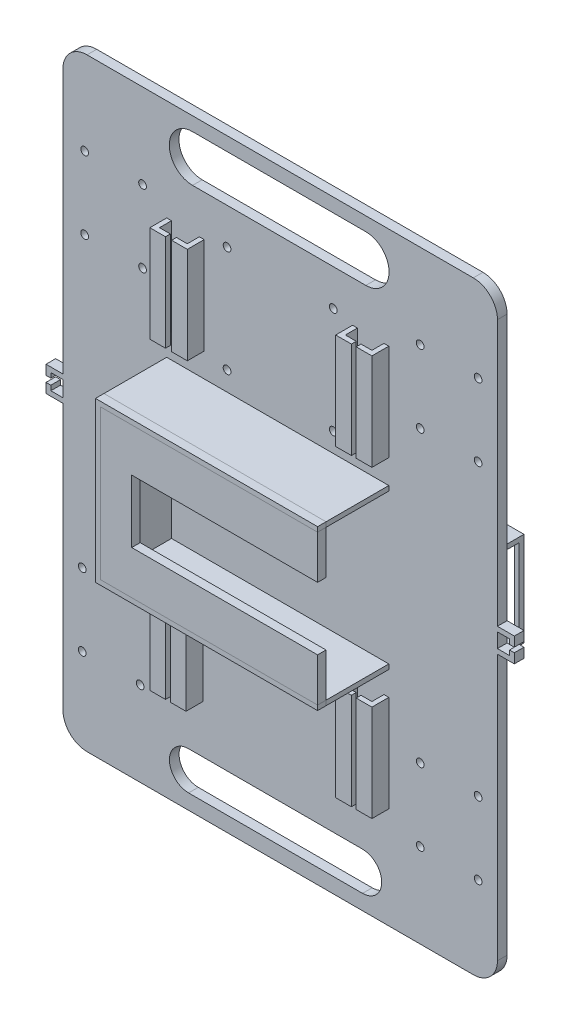
SolidWorks part; units mm, degrees
ref_plane "前视基准面" through (0, 0, 0) normal (0, 0, 1) x (1, 0, 0)
ref_plane "上视基准面" through (0, 0, 0) normal (0, 1, 0) x (1, 0, 0)
ref_plane "右视基准面" through (0, 0, 0) normal (1, 0, 0) x (0, 0, -1)
sketch "草图2" plane through (0, 0, 0) normal (0, 0, 1) x (1, 0, 0)
  line L0 (-107.1807, -135.5134) -> (-66.1807, -135.5134) construction
  line L1 (-97.1807, 63.077) -> (62.8193, 63.077)
  line L2 (-107.1807, 53.077) -> (-107.1807, -176.923)
  line L3 (-97.1807, -186.923) -> (62.8193, -186.923)
  line L4 (72.8193, 53.077) -> (72.8193, -176.923)
  line L5 (-92.3948, -186.923) -> (-92.3948, -116.923) construction
  line L6 (-85.9477, -186.923) -> (-85.9477, -156.923) construction
  line L7 (-107.1807, -156.923) -> (-66.1807, -156.923) construction
  line L8 (-107.1807, -116.923) -> (-66.1807, -116.923) construction
  line L9 (-66.1807, -116.923) -> (-66.1807, -156.923) construction
  line L10 (-66.1807, -156.923) -> (-107.1807, -156.923) construction
  line L11 (-107.1807, -156.923) -> (-107.1807, -116.923) construction
  line L12 (-107.1807, -156.923) -> (-107.1807, -158.923) construction
  line L13 (-107.1807, -152.2152) -> (-99.1807, -152.2152) construction
  line L14 (-99.1807, -156.923) -> (-99.1807, -151.923) construction
  line L15 (-99.1807, -151.923) -> (-99.1807, -121.923) construction
  line L16 (-99.1807, -121.923) -> (-75.1807, -121.923) construction
  line L17 (-75.1807, -121.923) -> (-75.1807, -151.923) construction
  line L18 (-66.1807, -156.923) -> (72.8193, -156.923) construction
  line L19 (-99.1807, -151.923) -> (72.8193, -151.923) construction
  line L20 (-99.1807, -121.923) -> (72.8193, -121.923) construction
  line L21 (72.8193, -151.923) -> (64.8193, -151.923) construction
  line L22 (64.8193, -151.923) -> (40.8193, -151.923) construction
  line L23 (40.8193, -151.923) -> (40.8193, -121.923) construction
  line L24 (40.8193, -121.923) -> (64.8193, -121.923) construction
  line L25 (64.8193, -121.923) -> (64.8193, -151.923) construction
  line L26 (-97.1807, 63.077) -> (-97.1807, 33.077) construction
  line L27 (-97.1807, 33.077) -> (-97.1807, -6.923) construction
  line L28 (-107.1807, 33.077) -> (-98.1807, 33.077) construction
  line L29 (-98.1807, 33.077) -> (-98.1807, 28.077) construction
  line L30 (-98.1807, 28.077) -> (-98.1807, -1.923) construction
  line L31 (-98.1807, 28.077) -> (-74.1807, 28.077) construction
  line L32 (-74.1807, 28.077) -> (-74.1807, -1.923) construction
  line L33 (-98.1807, -1.923) -> (-74.1807, -1.923) construction
  line L34 (-74.1807, 28.077) -> (72.8193, 28.077) construction
  line L35 (-74.1807, -1.923) -> (72.8193, -1.923) construction
  line L36 (40.8193, -121.923) -> (40.8193, 28.077) construction
  line L37 (64.8193, -121.923) -> (64.8193, 28.077) construction
  arc A0 (-97.1807, 63.077) -> (-107.1807, 53.077) centre (-97.1807, 53.077) ccw
  arc A1 (62.8193, 63.077) -> (72.8193, 53.077) centre (62.8193, 53.077) cw
  arc A2 (-107.1807, -176.923) -> (-97.1807, -186.923) centre (-97.1807, -176.923) ccw
  arc A3 (62.8193, -186.923) -> (72.8193, -176.923) centre (62.8193, -176.923) ccw
  circle A5 centre (-99.1807, -151.923) radius 1.6
  circle A6 centre (-99.1807, -121.923) radius 1.6
  circle A7 centre (-75.1807, -121.923) radius 1.6
  circle A8 centre (-75.1807, -151.923) radius 1.6
  circle A9 centre (64.8193, -151.923) radius 1.6
  circle A10 centre (40.8193, -151.923) radius 1.6
  circle A11 centre (40.8193, -121.923) radius 1.6
  circle A12 centre (64.8193, -121.923) radius 1.6
  circle A13 centre (-98.1807, 28.077) radius 1.6
  circle A14 centre (-98.1807, -1.923) radius 1.6
  circle A15 centre (-74.1807, 28.077) radius 1.6
  circle A16 centre (-74.1807, -1.923) radius 1.6
  circle A17 centre (40.8193, 28.077) radius 1.6
  circle A18 centre (64.8193, 28.077) radius 1.6
  circle A19 centre (40.8193, -1.923) radius 1.6
  circle A20 centre (64.8193, -1.923) radius 1.6
  point P6 (-107.1807, 63.077)
  point P9 (72.8193, 63.077)
  point P12 (-107.1807, -186.923)
  dimension "D3" = 10
  dimension "D4" = 10
  dimension "D5" = 10
  dimension "D6" = 10
  dimension "D13" = 30
  dimension "D14" = 24
  dimension "D15" = 8
  dimension "D16" = 24
  dimension "D17" = 30
  dimension "D21" = 30
  dimension "D22" = 24
  dimension "D1" = 180
  dimension "D2" = 250
  dimension "D7" = 41
  dimension "D8" = 70
  dimension "D9" = 30
  dimension "D10" = 41
  dimension "D11" = 8
  dimension "D12" = 5
  dimension "D18" = 40
  dimension "D19" = 9
  dimension "D20" = 5
extrude "凸台-拉伸1" add sketch "草图2" along normal blind 4
sketch "草图3" plane through (0, 0, 4) normal (0, 0, 1) x (1, 0, 0)
  line L0 (-17.1807, 63.077) -> (-17.1807, -186.923) construction
  line L1 (62.8193, 63.077) -> (-97.1807, 63.077) construction
  line L2 (-97.1807, -186.923) -> (62.8193, -186.923) construction
  line L3 (-107.1807, -61.923) -> (72.8193, -61.923) construction
  line L4 (-107.1807, 53.077) -> (-107.1807, -176.923) construction
  line L5 (72.8193, -176.923) -> (72.8193, 53.077) construction
  line L6 (-17.1807, -61.923) -> (-17.1807, -30.923) construction
  line L7 (-17.1807, -61.923) -> (-17.1807, -92.923) construction
  line L8 (-17.1807, -61.923) -> (27.8193, -61.923) construction
  line L9 (-17.1807, -61.923) -> (-62.1807, -61.923) construction
  line L10 (-17.1807, -30.923) -> (27.8193, -30.923) construction
  line L11 (27.8193, -30.923) -> (27.8193, -92.923) construction
  line L12 (27.8193, -92.923) -> (-62.1807, -92.923) construction
  line L13 (-62.1807, -92.923) -> (-62.1807, -30.923) construction
  line L14 (-62.1807, -30.923) -> (-17.1807, -30.923) construction
  line L15 (27.8193, -30.923) -> (-62.1807, -30.923)
  line L16 (-62.1807, -30.923) -> (-62.1807, -92.923)
  line L17 (-62.1807, -92.923) -> (27.8193, -92.923)
  line L18 (27.8193, -30.923) -> (27.8193, -28.923) construction
  line L19 (-62.1807, -30.923) -> (-64.1807, -30.923) construction
  line L20 (-62.1807, -92.923) -> (-62.1807, -94.923) construction
  line L21 (27.8193, -30.923) -> (27.8193, -28.923)
  line L22 (27.8193, -28.923) -> (-64.1807, -28.923)
  line L23 (-64.1807, -28.923) -> (-64.1807, -94.923)
  line L24 (-64.1807, -94.923) -> (27.8193, -94.923)
  line L25 (27.8193, -94.923) -> (27.8193, -92.923)
  dimension "D1" = 31
  dimension "D2" = 45
  dimension "D3" = 45
  dimension "D4" = 2
  dimension "D5" = 2
extrude "凸台-拉伸2" add sketch "草图3" along normal blind 26 contours L22 L23 L24 L25 L17 L16 L15 L21
sketch "草图5" plane through (0, 0, 30) normal (0, 0, 1) x (1, 0, 0)
  line L0 (-18.1807, -28.923) -> (-18.1807, -48.923) construction
  line L1 (27.8193, -28.923) -> (-64.1807, -28.923) construction
  line L2 (-18.1807, -94.923) -> (-18.1807, -74.923) construction
  line L3 (-64.1807, -94.923) -> (27.8193, -94.923) construction
  line L4 (27.8193, -28.923) -> (27.8193, -48.923)
  line L5 (27.8193, -48.923) -> (-64.1807, -48.923)
  line L6 (-64.1807, -28.923) -> (-64.1807, -94.923) construction
  line L7 (-64.1807, -48.923) -> (-64.1807, -28.923)
  line L8 (-64.1807, -28.923) -> (27.8193, -28.923)
  line L9 (27.8193, -94.923) -> (27.8193, -74.923)
  line L10 (27.8193, -74.923) -> (-64.1807, -74.923)
  line L11 (-64.1807, -28.923) -> (-64.1807, -94.923) construction
  line L12 (-64.1807, -74.923) -> (-64.1807, -94.923)
  line L13 (-64.1807, -94.923) -> (27.8193, -94.923)
  line L14 (-64.1807, -61.923) -> (-49.1807, -61.923) construction
  line L15 (-64.1807, -48.923) -> (-64.1807, -74.923)
  line L16 (-49.1807, -74.923) -> (-49.1807, -48.923)
  line L17 (-49.1807, -48.923) -> (-64.1807, -48.923)
  line M11 (27.8193, -92.923) -> (-62.1807, -92.923)
  line M12 (-62.1807, -92.923) -> (-62.1807, -30.923)
  line M13 (-62.1807, -30.923) -> (27.8193, -30.923)
  dimension "D1" = 15
extrude "凸台-拉伸3" add sketch "草图5" along normal blind 3.5 separate body contours L5 L4 M13 M12 | L9 L10 M12 M11 | L10 L16 L5 M12
sketch "草图6" plane through (0, 0, 33.5) normal (0, 0, 1) x (1, 0, 0)
  line L0 (27.8193, -30.923) -> (27.8193, -28.923)
  line L1 (27.8193, -28.923) -> (-64.1807, -28.923)
  line L2 (-64.1807, -28.923) -> (-64.1807, -94.923)
  line L3 (-64.1807, -94.923) -> (27.8193, -94.923)
  line L4 (27.8193, -94.923) -> (27.8193, -92.923)
  line L5 (27.8193, -92.923) -> (-62.1807, -92.923)
  line L6 (-62.1807, -92.923) -> (-62.1807, -30.923)
  line L7 (-62.1807, -30.923) -> (27.8193, -30.923)
extrude "凸台-拉伸4" add sketch "草图6" against normal blind 3.5 separate body
sketch "草图7" plane through (0, 0, 4) normal (0, 0, 1) x (1, 0, 0)
  line L0 (-64.1807, -94.923) -> (-64.1807, -104.923) construction
  line L1 (27.8193, -94.923) -> (27.8193, -104.923) construction
  line L2 (-64.1807, -104.923) -> (-64.1807, -144.923) construction
  line L3 (27.8193, -104.923) -> (27.8193, -144.923) construction
  line L4 (-64.1807, -104.923) -> (-62.1807, -104.923) construction
  line L5 (-62.1807, -104.923) -> (-62.1807, -144.923) construction
  line L6 (-62.1807, -144.923) -> (-64.1807, -144.923) construction
  line L7 (-64.1807, -144.923) -> (-64.1807, -104.923) construction
  line L8 (27.8193, -104.923) -> (25.8193, -104.923) construction
  line L9 (25.8193, -104.923) -> (25.8193, -144.923) construction
  line L10 (25.8193, -144.923) -> (27.8193, -144.923) construction
  line L11 (27.8193, -144.923) -> (27.8193, -104.923) construction
  line L12 (-64.1807, -104.923) -> (-49.1807, -104.923) construction
  line L13 (-49.1807, -104.923) -> (-49.1807, -144.923) construction
  line L14 (-49.1807, -144.923) -> (-51.1807, -144.923) construction
  line L15 (-51.1807, -144.923) -> (-51.1807, -104.923) construction
  line L16 (27.8193, -104.923) -> (12.8193, -104.923) construction
  line L17 (12.8193, -104.923) -> (12.8193, -144.923) construction
  line L18 (12.8193, -144.923) -> (27.8193, -144.923) construction
  line L19 (12.8193, -104.923) -> (14.8193, -104.923) construction
  line L20 (14.8193, -104.923) -> (14.8193, -144.923) construction
  line L21 (-64.1807, -104.923) -> (-62.1807, -104.923)
  line L22 (-62.1807, -104.923) -> (-62.1807, -144.923)
  line L23 (-62.1807, -144.923) -> (-64.1807, -144.923)
  line L24 (-64.1807, -144.923) -> (-64.1807, -104.923)
  line L25 (-51.1807, -104.923) -> (-51.1807, -144.923)
  line L26 (-51.1807, -144.923) -> (-49.1807, -144.923)
  line L27 (-49.1807, -144.923) -> (-49.1807, -104.923)
  line L28 (-49.1807, -104.923) -> (-51.1807, -104.923)
  line L29 (12.8193, -104.923) -> (12.8193, -144.923)
  line L30 (12.8193, -144.923) -> (14.8193, -144.923)
  line L31 (14.8193, -144.923) -> (14.8193, -104.923)
  line L32 (14.8193, -104.923) -> (12.8193, -104.923)
  line L33 (25.8193, -104.923) -> (27.8193, -104.923)
  line L34 (27.8193, -104.923) -> (27.8193, -144.923)
  line L35 (27.8193, -144.923) -> (25.8193, -144.923)
  line L36 (25.8193, -144.923) -> (25.8193, -104.923)
  dimension "D1" = 10
  dimension "D2" = 40
extrude "凸台-拉伸5" add sketch "草图7" along normal blind 5
sketch "草图8" plane through (0, 0, 9) normal (0, 0, 1) x (1, 0, 0)
  line L0 (-64.1807, -104.923) -> (-57.6807, -104.923)
  line L1 (-57.6807, -104.923) -> (-57.6807, -144.923)
  line L2 (-57.6807, -144.923) -> (-64.1807, -144.923)
  line L3 (-64.1807, -144.923) -> (-64.1807, -104.923)
  line L4 (-49.1807, -104.923) -> (-55.6807, -104.923)
  line L5 (-55.6807, -104.923) -> (-55.6807, -144.923)
  line L6 (-55.6807, -144.923) -> (-49.1807, -144.923)
  line L7 (-49.1807, -144.923) -> (-49.1807, -104.923)
  line L8 (12.8193, -104.923) -> (19.3193, -104.923)
  line L9 (19.3193, -104.923) -> (19.3193, -144.923)
  line L10 (19.3193, -144.923) -> (12.8193, -144.923)
  line L11 (12.8193, -144.923) -> (12.8193, -104.923)
  line L12 (27.8193, -104.923) -> (21.3193, -104.923)
  line L13 (21.3193, -144.923) -> (27.8193, -144.923)
  line L14 (27.8193, -144.923) -> (27.8193, -104.923)
  line L15 (21.3193, -104.923) -> (21.3193, -144.923)
extrude "凸台-拉伸6" add sketch "草图8" along normal blind 2
ref_plane "基准面1" through (-57.6807, -144.923, 9) normal (0, 0, -1) x (-1, 0, 0)
sketch "草图11" plane through (0, 0, 4) normal (0, 0, 1) x (1, 0, 0)
  line L0 (-64.1807, -28.923) -> (-64.1807, -18.923) construction
  line L1 (27.8193, -28.923) -> (27.8193, -18.923) construction
  line L2 (-64.1807, -18.923) -> (-64.1807, 21.077)
  line L3 (-64.1807, 21.077) -> (-62.1807, 21.077)
  line L4 (-62.1807, 21.077) -> (-62.1807, -18.923)
  line L5 (-62.1807, -18.923) -> (-64.1807, -18.923) construction
  line L6 (-64.1807, 21.077) -> (-48.649, 21.077) construction
  line L7 (-48.649, 21.077) -> (-50.649, 21.077)
  line L8 (-50.649, 21.077) -> (-50.649, -18.923)
  line L9 (-50.649, -18.923) -> (-48.649, -18.923)
  line L10 (-48.649, -18.923) -> (-48.649, 21.077)
  line L11 (27.8193, -18.923) -> (27.8193, 21.077)
  line L12 (27.8193, 21.077) -> (25.8193, 21.077)
  line L13 (25.8193, 21.077) -> (25.8193, -18.923)
  line L14 (25.8193, -18.923) -> (27.8193, -18.923)
  line L15 (27.8193, 21.077) -> (12.8193, 21.077) construction
  line L16 (12.8193, 21.077) -> (12.8193, -18.923)
  line L17 (12.8193, -18.923) -> (14.8193, -18.923)
  line L18 (14.8193, -18.923) -> (14.8193, 21.077)
  line L19 (14.8193, 21.077) -> (12.8193, 21.077)
extrude "凸台-拉伸7" add sketch "草图11" along normal blind 5 contours L10 L7 L8 L9 | L16 L17 L18 L19 | L13 L14 L11 L12
sketch "草图12" plane through (0, 0, 4) normal (0, 0, 1) x (1, 0, 0)
  line L0 (-64.1807, -28.923) -> (-64.1807, 21.077) construction
  line L1 (-64.1807, 21.077) -> (-62.1807, 21.077)
  line L2 (-62.1807, 21.077) -> (-62.1807, -18.923)
  line L3 (-62.1807, -18.923) -> (-64.1807, -18.923)
  line L4 (-64.1807, -18.923) -> (-64.1807, 21.077)
extrude "凸台-拉伸8" add sketch "草图12" along normal blind 5
sketch "草图13" plane through (0, 0, 9) normal (0, 0, 1) x (1, 0, 0)
  line L0 (-64.1807, 21.077) -> (-57.6807, 21.077)
  line L1 (-57.6807, 21.077) -> (-57.6807, -18.923)
  line L2 (-57.6807, -18.923) -> (-64.1807, -18.923)
  line L3 (-64.1807, 21.077) -> (-64.1807, -18.923) construction
  line L4 (-64.1807, -18.923) -> (-62.1807, -18.923) construction
  line L5 (-64.1807, -18.923) -> (-64.1807, 21.077)
extrude "凸台-拉伸9" add sketch "草图13" along normal blind 2
sketch "草图14" plane through (0, 0, 9) normal (0, 0, 1) x (1, 0, 0)
  line L0 (-48.649, 21.077) -> (-48.649, -18.923)
  line L1 (-48.649, -18.923) -> (-55.149, -18.923)
  line L2 (-55.149, -18.923) -> (-55.149, 21.077)
  line L3 (-55.149, 21.077) -> (-48.649, 21.077)
  line L4 (27.8193, -18.923) -> (21.3193, -18.923)
  line L5 (21.3193, -18.923) -> (21.3193, 21.077)
  line L6 (21.3193, 21.077) -> (27.8193, 21.077)
  line L7 (27.8193, 21.077) -> (27.8193, -18.923)
  line L8 (12.8193, -18.923) -> (19.3193, -18.923)
  line L9 (19.3193, -18.923) -> (19.3193, 21.077)
  line L10 (19.3193, 21.077) -> (12.8193, 21.077)
  line L11 (12.8193, 21.077) -> (12.8193, -18.923)
extrude "凸台-拉伸10" add sketch "草图14" along normal blind 2
sketch "草图16" plane through (0, 0, 0) normal (0, 0, -1) x (-1, 0, 0)
  line L0 (17.1807, 63.077) -> (17.1807, 23.077) construction
  line L1 (-62.8193, 63.077) -> (97.1807, 63.077) construction
  line L2 (17.1807, 23.077) -> (39.1807, 23.077) construction
  line L3 (17.1807, 23.077) -> (-4.8193, 23.077) construction
  line L4 (-4.8193, 23.077) -> (-4.8193, -20.923) construction
  line L5 (-4.8193, -20.923) -> (39.1807, -20.923) construction
  line L6 (39.1807, -20.923) -> (39.1807, 23.077) construction
  circle A0 centre (-4.8193, 23.077) radius 1.6
  circle A1 centre (39.1807, 23.077) radius 1.6
  circle A2 centre (39.1807, -20.923) radius 1.6
  circle A3 centre (-4.8193, -20.923) radius 1.6
extrude "切除-拉伸1" cut sketch "草图16" against normal blind 5
sketch "草图19" plane through (0, 0, 0) normal (0, 0, -1) x (-1, 0, 0)
  line L0 (-72.8193, -61.923) -> (107.1807, -61.923) construction
  line L1 (-72.8193, -176.923) -> (-72.8193, 53.077) construction
  line L2 (107.1807, 53.077) -> (107.1807, -176.923) construction
  line L3 (-72.8193, -61.923) -> (-32.7734, -61.923) construction
sketch "草图20" plane through (0, 0, 0) normal (0, 0, -1) x (-1, 0, 0)
  line L0 (-72.8193, -61.923) -> (-57.8193, -61.923) construction
  line L1 (-72.8193, -61.923) -> (107.1807, -61.923) construction
  line L2 (-57.8193, -61.923) -> (-22.8193, -61.923) construction
  line L3 (-22.8193, -61.923) -> (-22.8193, -44.423) construction
  line L4 (-22.8193, -61.923) -> (-22.8193, -79.423) construction
  line L5 (-22.8193, -79.423) -> (-57.8193, -79.423)
  line L6 (-57.8193, -79.423) -> (-57.8193, -44.423)
  line L7 (-57.8193, -44.423) -> (-22.8193, -44.423)
  line L8 (-22.8193, -44.423) -> (-22.8193, -79.423)
  line L9 (-22.8193, -44.423) -> (-22.8193, -42.423) construction
  line L10 (-57.8193, -44.423) -> (-59.8193, -44.423) construction
  line L11 (-57.8193, -79.423) -> (-57.8193, -81.423) construction
  line L12 (-22.8193, -79.423) -> (-20.8193, -79.423) construction
  line L13 (-22.8193, -42.423) -> (-59.8193, -42.423)
  line L14 (-59.8193, -42.423) -> (-59.8193, -81.423)
  line L15 (-59.8193, -81.423) -> (-20.8193, -81.423)
  line L16 (-20.8193, -81.423) -> (-20.8193, -42.423)
  line L17 (-20.8193, -42.423) -> (-22.8193, -42.423)
  dimension "D1" = 15
extrude "凸台-拉伸12" add sketch "草图20" along normal blind 20
sketch "草图21" plane through (20.8193, 0, 0) normal (-1, 0, 0) x (0, 0, 1)
  line L0 (0, -42.423) -> (0, -44.423) construction
  line L1 (0, 53.077) -> (0, -176.923) construction
  line L2 (0, -81.423) -> (0, -79.423) construction
  line L3 (0, -44.423) -> (-18, -44.423) construction
  line L4 (-18, -44.423) -> (-18, -79.423) construction
  line L5 (-18, -79.423) -> (0, -79.423) construction
  line L7 (0, -44.423) -> (-18, -44.423)
  line L8 (0, -44.423) -> (0, -79.423)
  line L9 (0, -79.423) -> (-18, -79.423)
  line L10 (-18, -44.423) -> (-18, -79.423)
extrude "切除-拉伸2" cut sketch "草图21" against normal blind 60
sketch "草图22" plane through (59.8193, 0, 0) normal (1, 0, 0) x (0, 0, -1)
  line L0 (18, -79.423) -> (0, -79.423) construction
  line L1 (0, -44.423) -> (3, -44.423)
  line L2 (0, -44.423) -> (0, -79.423)
  line L3 (0, -79.423) -> (3, -79.423)
  line L4 (3, -44.423) -> (3, -79.423)
  dimension "D1" = 3
extrude "凸台-拉伸13" add sketch "草图22" against normal blind 1
sketch "草图23" plane through (20.8193, 0, 0) normal (-1, 0, 0) x (0, 0, 1)
  line L1 (0, -44.423) -> (-3, -44.423)
  line L2 (0, -44.423) -> (0, -79.423)
  line L3 (0, -79.423) -> (-3, -79.423)
  line L4 (-3, -44.423) -> (-3, -79.423)
extrude "凸台-拉伸18" add sketch "草图23" against normal blind 1
sketch "草图24" plane through (0, 0, 0) normal (0, 0, -1) x (-1, 0, 0)
  line L0 (107.1807, -61.923) -> (92.1807, -61.923) construction
  line L1 (-72.8193, -61.923) -> (107.1807, -61.923) construction
  line L2 (92.1807, -61.923) -> (92.1807, -44.423) construction
  line L3 (92.1807, -44.423) -> (57.1807, -44.423) construction
  line L4 (57.1807, -44.423) -> (57.1807, -79.423) construction
  line L5 (57.1807, -79.423) -> (92.1807, -79.423) construction
  line L6 (92.1807, -79.423) -> (92.1807, -61.923) construction
  line L7 (92.1807, -44.423) -> (92.1807, -42.423) construction
  line L8 (92.1807, -44.423) -> (57.1807, -44.423)
  line L9 (92.1807, -44.423) -> (92.1807, -79.423)
  line L10 (92.1807, -79.423) -> (57.1807, -79.423)
  line L11 (57.1807, -44.423) -> (57.1807, -79.423)
  line L12 (92.1807, -44.423) -> (94.1807, -44.423) construction
  line L14 (93.8137, -42.423) -> (54.8137, -42.423)
  line L15 (93.8137, -42.423) -> (93.8137, -81.423)
  line L16 (93.8137, -81.423) -> (54.8137, -81.423)
  line L17 (54.8137, -42.423) -> (54.8137, -81.423)
  dimension "D1" = 39
  dimension "D2" = 39
extrude "凸台-拉伸19" add sketch "草图24" along normal blind 20
sketch "草图25" plane through (-93.8137, 0, 0) normal (-1, 0, 0) x (0, 0, 1)
  line L0 (0, -42.423) -> (-3, -42.423) construction
  line L1 (-20, -42.423) -> (0, -42.423) construction
  line L2 (0, -81.423) -> (-3, -81.423) construction
  line L3 (-20, -81.423) -> (0, -81.423) construction
  line L4 (-3, -81.423) -> (-3, -76.423) construction
  line L5 (-3, -42.423) -> (-3, -44.423) construction
  line L6 (-20, -44.423) -> (-15, -44.423)
  line L7 (-20, -76.423) -> (-15, -76.423) construction
  line L8 (-20, -81.423) -> (-20, -42.423) construction
  line L10 (-15, -44.423) -> (-3, -44.423)
  line L11 (-15, -44.423) -> (-15, -76.423)
  line L12 (-15, -76.423) -> (-3, -76.423)
  line L13 (-3, -44.423) -> (-3, -76.423)
  dimension "D1" = 5
extrude "切除-拉伸3" cut sketch "草图25" against normal blind 50 contours L13 L10 L11 L12
sketch "草图26" plane through (72.8193, 0, 0) normal (1, 0, 0) x (0, 0, -1)
  line L0 (-4, -56.923) -> (0, -56.923)
  line L1 (0, -42.423) -> (0, -81.423) construction
  line L2 (0, -176.923) -> (0, 53.077) construction
  line L3 (0, -61.923) -> (0, -66.923) construction
  line L4 (0, -56.923) -> (-4, -56.923) construction
  line L5 (-4, -176.923) -> (-4, 53.077) construction
  line L6 (-4, -56.923) -> (-4, -58.923) construction
  line L7 (0, -66.923) -> (-4, -66.923) construction
  line L8 (-4, -66.923) -> (-4, -64.923) construction
  line L9 (0, -58.923) -> (-4, -58.923)
  line L13 (0, -56.923) -> (0, -58.923)
  line L14 (0, -66.923) -> (-4, -66.923)
  line L15 (0, -66.923) -> (0, -64.923)
  line L16 (0, -64.923) -> (-4, -64.923)
  line L17 (-4, -66.923) -> (-4, -64.923)
  line L18 (-4, -58.923) -> (-4, -56.923)
extrude "凸台-拉伸20" add sketch "草图26" along normal blind 5
sketch "草图27" plane through (77.8193, 0, 0) normal (1, 0, 0) x (0, 0, -1)
  line L0 (-4, -56.923) -> (-4, -60.923)
  line L1 (-4, -64.923) -> (-4, -58.923) construction
  line L2 (-4, -60.923) -> (0, -60.923)
  line L3 (0, -64.923) -> (0, -58.923) construction
  line L4 (0, -60.923) -> (0, -56.923)
  line L5 (0, -56.923) -> (-4, -56.923)
  line L6 (-4, -66.923) -> (-4, -62.923)
  line L7 (-4, -62.923) -> (0, -62.923)
  line L8 (0, -42.423) -> (0, -81.423) construction
  line L9 (0, -62.923) -> (0, -66.923)
  line L10 (0, -66.923) -> (-4, -66.923)
extrude "凸台-拉伸21" add sketch "草图27" along normal blind 2
sketch "草图28" plane through (-107.1807, 0, 0) normal (-1, 0, 0) x (0, 0, 1)
  line L0 (0, -61.923) -> (0, -56.402) construction
  line L2 (0, -81.423) -> (0, -42.423) construction
  line L3 (0, -61.923) -> (0, -66.923) construction
  line L4 (0, -56.402) -> (0, -58.402)
  line L5 (0, -58.402) -> (4, -58.402)
  line L6 (4, -28.923) -> (4, -94.923) construction
  line L7 (4, -58.402) -> (4, -56.402)
  line L8 (4, -56.402) -> (0, -56.402)
  line L9 (0, -66.923) -> (0, -64.923)
  line L10 (0, -64.923) -> (4, -64.923)
  line L11 (4, 53.077) -> (4, -176.923) construction
  line L12 (4, -64.923) -> (4, -66.923)
  line L13 (4, -66.923) -> (0, -66.923)
extrude "凸台-拉伸22" add sketch "草图28" along normal blind 5
sketch "草图29" plane through (-112.1807, 0, 0) normal (-1, 0, 0) x (0, 0, 1)
  line L0 (0, -56.402) -> (0, -60.402)
  line L1 (0, -58.402) -> (0, -64.923) construction
  line L2 (0, -60.402) -> (4, -60.402)
  line L3 (4, -58.402) -> (4, -64.923) construction
  line L4 (4, -60.402) -> (4, -56.402)
  line L5 (4, -56.402) -> (0, -56.402)
  line L6 (0, -66.923) -> (0, -62.923)
  line L7 (0, -62.923) -> (4, -62.923)
  line L8 (4, -62.923) -> (4, -66.923)
  line L9 (4, -28.923) -> (4, -94.923) construction
  line L10 (4, -66.923) -> (0, -66.923)
extrude "凸台-拉伸23" add sketch "草图29" along normal blind 2
sketch "草图31" plane through (0, 0, 0) normal (0, 0, -1) x (-1, 0, 0)
  line L0 (17.1807, 63.077) -> (17.1807, -186.923) construction
  line L1 (-62.8193, 63.077) -> (97.1807, 63.077) construction
  line L2 (97.1807, -186.923) -> (-62.8193, -186.923) construction
sketch "草图33" plane through (0, 0, 4) normal (0, 0, 1) x (1, 0, 0)
  line L0 (-53.4785, 47.7407) -> (18.307, 47.7407) construction
  line L1 (-53.4785, 57.3732) -> (18.307, 57.3732)
  line L2 (-53.4785, 38.1081) -> (18.307, 38.1081)
  line L3 (-55.1285, -172.7462) -> (16.9321, -172.7462) construction
  line L4 (-55.1285, -164.8151) -> (16.9321, -164.8151)
  line L5 (-55.1285, -180.6774) -> (16.9321, -180.6774)
  arc A0 (-53.4785, 57.3732) -> (-53.4785, 38.1081) centre (-53.4785, 47.7407) ccw
  arc A1 (18.307, 38.1081) -> (18.307, 57.3732) centre (18.307, 47.7407) ccw
  arc A2 (-55.1285, -164.8151) -> (-55.1285, -180.6774) centre (-55.1285, -172.7462) ccw
  arc A3 (16.9321, -180.6774) -> (16.9321, -164.8151) centre (16.9321, -172.7462) ccw
  point P2 (-17.5857, 47.7407)
  point P7 (-19.0982, -172.7462)
extrude "切除-拉伸4" cut sketch "草图33" against normal blind 10
